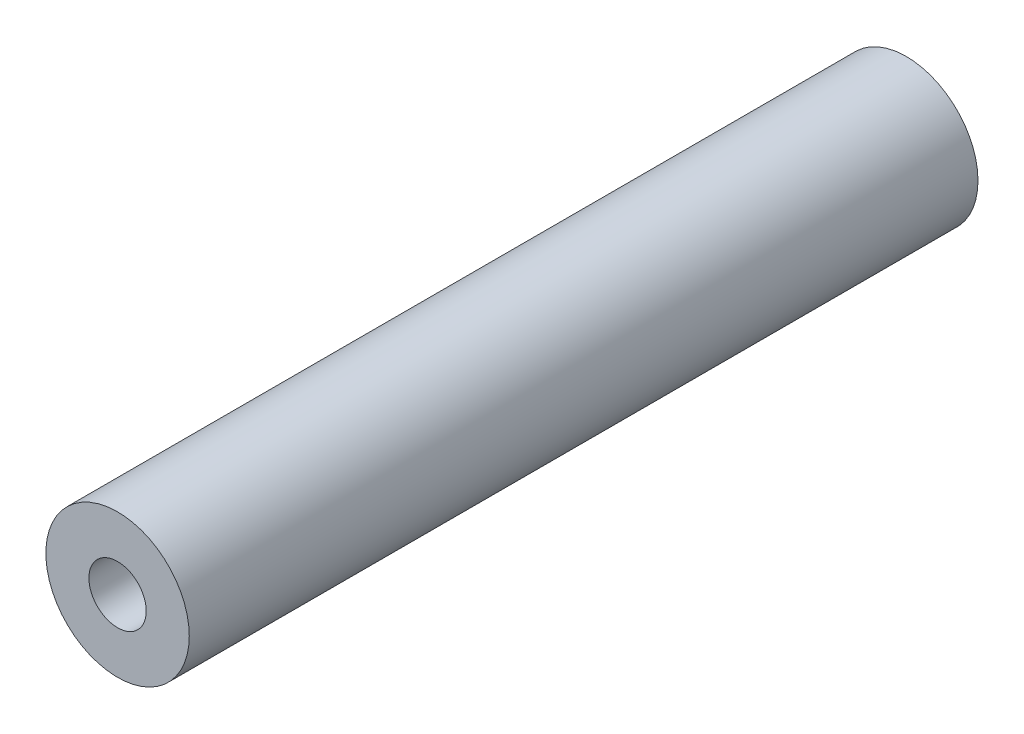
SolidWorks part; units mm, degrees
ref_plane "Front Plane" through (0, 0, 0) normal (0, 0, 1) x (1, 0, 0)
ref_plane "Top Plane" through (0, 0, 0) normal (0, 1, 0) x (1, 0, 0)
ref_plane "Right Plane" through (0, 0, 0) normal (1, 0, 0) x (0, 0, -1)
sketch "Sketch1" plane through (0, 0, 0) normal (0, 0, 1) x (1, 0, 0)
  line L0 (0, 0) -> (0, -87.5) construction
  line L1 (0, 0) -> (75.7772, -43.75) construction
  circle A0 centre (0, 0) radius 87.5 construction
  circle A1 centre (0, -65) radius 5
  circle A2 centre (0, -65) radius 2
  dimension "D2" = 10
  dimension "D3" = 4
  dimension "D1" = 60
  dimension "D4" = 65
extrude "Boss-Extrude1" add sketch "Sketch1" along normal blind 55
